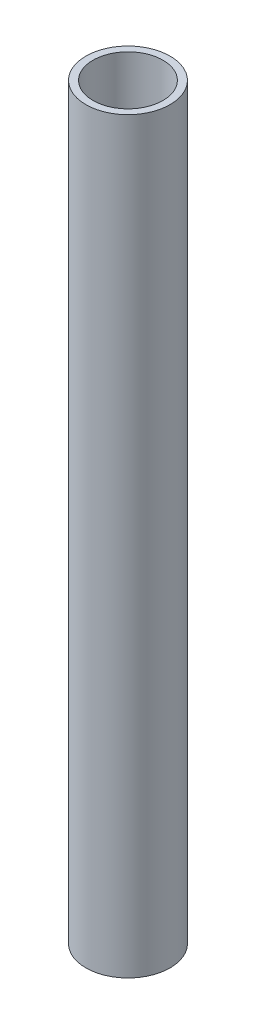
SolidWorks part; units mm, degrees
material "6061-T6 (SS)"
ref_plane "Front Plane" through (0, 0, 0) normal (0, 0, 1) x (1, 0, 0)
ref_plane "Top Plane" through (0, 0, 0) normal (0, 1, 0) x (1, 0, 0)
ref_plane "Right Plane" through (0, 0, 0) normal (1, 0, 0) x (0, 0, -1)
sketch "Sketch1" plane through (0, 0, 0) normal (0, 1, 0) x (1, 0, 0)
  circle A0 centre (0, 0) radius 21.082
  circle A1 centre (0, 0) radius 17.526
  dimension "D1" = 42.164
  dimension "D2" = 35.052
extrude "Boss-Extrude1" add sketch "Sketch1" along normal blind 374.65
